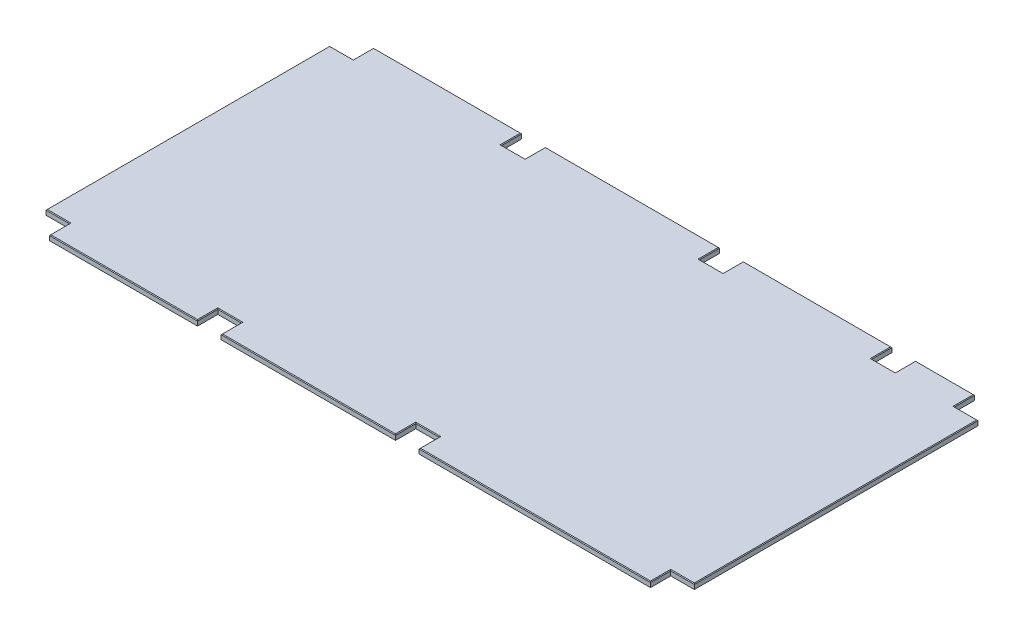
SolidWorks part; units mm, degrees
material "Oak"
ref_plane "Front Plane" through (0, 0, 0) normal (0, 0, 1) x (1, 0, 0)
ref_plane "Top Plane" through (0, 0, 0) normal (0, 1, 0) x (1, 0, 0)
ref_plane "Right Plane" through (0, 0, 0) normal (1, 0, 0) x (0, 0, -1)
sketch "Sketch1" plane through (0, 0, 0) normal (0, 1, 0) x (1, 0, 0)
  line L1 (0, 1219.2) -> (2438.4, 1219.2)
  line L2 (0, 1219.2) -> (0, 0)
  line L3 (0, 0) -> (2438.4, 0)
  line L4 (2438.4, 1219.2) -> (2438.4, 0)
  dimension "D1" = 1219.2
  dimension "D2" = 2438.4
extrude "Boss-Extrude1" add sketch "Sketch1" along normal mid plane 19.05
sketch "Sketch2" plane through (0, 9.525, 0) normal (0, 1, 0) x (1, 0, 0)
  line L5 (2438.4, 1219.2) -> (0, 1219.2) construction
  line L7 (0, 1219.2) -> (88.9, 1219.2)
  line L8 (0, 1219.2) -> (0, 1143)
  line L9 (0, 1143) -> (88.9, 1143)
  line L10 (88.9, 1219.2) -> (88.9, 1143)
  line L11 (646.1125, 1219.2) -> (735.0125, 1219.2)
  line L12 (646.1125, 1219.2) -> (646.1125, 1143)
  line L13 (646.1125, 1143) -> (735.0125, 1143)
  line L15 (2438.4, 0) -> (2438.4, 1219.2) construction
  line L18 (1390.6627, 1143) -> (1479.5627, 1143)
  line L19 (1479.5627, 1219.2) -> (1479.5627, 1143)
  line L20 (2038.35, 1219.2) -> (2127.25, 1219.2)
  line L21 (2038.35, 1219.2) -> (2038.35, 1143)
  line L22 (2038.35, 1143) -> (2127.25, 1143)
  line L23 (2127.25, 1219.2) -> (2127.25, 1143)
  line L24 (2349.5, 1219.2) -> (2438.4, 1219.2)
  line L25 (2349.5, 1219.2) -> (2349.5, 1143)
  line L26 (2349.5, 1143) -> (2438.4, 1143)
  line L27 (2438.4, 1219.2) -> (2438.4, 1143)
  line L28 (735.0125, 1219.2) -> (735.0125, 1143)
  line L29 (0, 1219.2) -> (0, 0) construction
  line L30 (1479.5627, 1219.2) -> (1390.6627, 1219.2)
  line L31 (1390.6627, 1219.2) -> (1390.6627, 1143)
  line L32 (0, 609.6) -> (2438.4, 609.6) construction
  line L33 (1390.6627, 0) -> (1390.6627, 76.2)
  line L34 (1479.5627, 0) -> (1390.6627, 0)
  line L35 (735.0125, 0) -> (735.0125, 76.2)
  line L36 (2438.4, 0) -> (2438.4, 76.2)
  line L37 (2349.5, 76.2) -> (2438.4, 76.2)
  line L38 (2349.5, 0) -> (2349.5, 76.2)
  line L39 (2349.5, 0) -> (2438.4, 0)
  line L44 (1479.5627, 0) -> (1479.5627, 76.2)
  line L45 (1390.6627, 76.2) -> (1479.5627, 76.2)
  line L46 (646.1125, 76.2) -> (735.0125, 76.2)
  line L47 (646.1125, 0) -> (646.1125, 76.2)
  line L48 (646.1125, 0) -> (735.0125, 0)
  line L49 (88.9, 0) -> (88.9, 76.2)
  line L50 (0, 76.2) -> (88.9, 76.2)
  line L51 (0, 0) -> (0, 76.2)
  line L52 (0, 0) -> (88.9, 0)
  point P25 (0, 1181.1)
  point P27 (1479.5627, 1181.1)
  dimension "D1" = 76.2
  dimension "D2" = 88.9
  dimension "D3" = 646.1125
  dimension "D4" = 735.0125
  dimension "D5" = 88.9
  dimension "D6" = 311.15
  dimension "D7" = 400.05
  dimension "D8" = 558.7873
  dimension "D9" = 88.9
extrude "Cut-Extrude1" cut sketch "Sketch2" against normal through all
chamfer "Chamfer1" distance 2.54 angle 45 32 edges at (0, 9.525, -609.6) (44.45, 9.525, -1143) (88.9, 9.525, -1181.1) (367.5062, 9.525, -1219.2) (646.1125, 9.525, -1181.1) (690.5625, 9.525, -1143) (735.0125, 9.525, -1181.1) (1062.8376, 9.525, -1219.2) (1390.6627, 9.525, -1181.1) (1435.1127, 9.525, -1143) (1479.5627, 9.525, -1181.1) (1758.9564, 9.525, -1219.2) (2038.35, 9.525, -1181.1) (2082.8, 9.525, -1143) (2127.25, 9.525, -1181.1) (2238.375, 9.525, -1219.2) (2349.5, 9.525, -1181.1) (2393.95, 9.525, -1143) (2438.4, 9.525, -609.6) (2393.95, 9.525, -76.2) (2349.5, 9.525, -38.1) (1914.5313, 9.525, 0) (1479.5627, 9.525, -38.1) (1435.1127, 9.525, -76.2) (1390.6627, 9.525, -38.1) (1062.8376, 9.525, 0) (735.0125, 9.525, -38.1) (690.5625, 9.525, -76.2) (646.1125, 9.525, -38.1) (367.5062, 9.525, 0) (88.9, 9.525, -38.1) (44.45, 9.525, -76.2)
